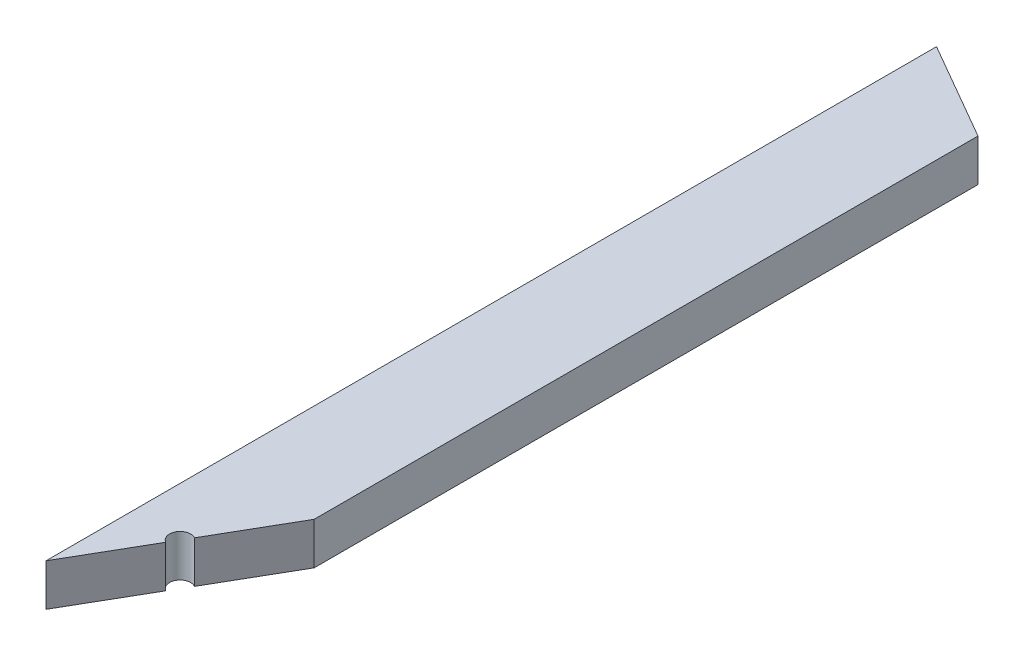
SolidWorks part; units mm, degrees
ref_plane "Front Plane" through (0, 0, 0) normal (0, 0, 1) x (1, 0, 0)
ref_plane "Top Plane" through (0, 0, 0) normal (0, 1, 0) x (1, 0, 0)
ref_plane "Right Plane" through (0, 0, 0) normal (1, 0, 0) x (0, 0, -1)
sketch "Sketch1" plane through (0, 0, 0) normal (0, 0, 1) x (1, 0, 0)
  line L1 (-44.45, -19.05) -> (44.45, -19.05)
  line L2 (-44.45, -19.05) -> (-44.45, 19.05)
  line L3 (-44.45, 19.05) -> (44.45, 19.05)
  line L4 (44.45, -19.05) -> (44.45, 19.05)
  line L5 (-44.45, -19.05) -> (44.45, 19.05) construction
  line L6 (-44.45, 19.05) -> (44.45, -19.05) construction
  point P0 (0, 0)
  dimension "D1" = 38.1
  dimension "D2" = 88.9
extrude "Boss-Extrude1" add sketch "Sketch1" along normal blind 806.5592
sketch "Sketch2" plane through (0, 19.05, 0) normal (0, 1, 0) x (1, 0, 0)
  line L0 (-44.45, 0) -> (44.45, 0)
  line L1 (44.45, 0) -> (44.45, -51.3264)
  line L2 (44.45, -806.5592) -> (44.45, 0) construction
  line L3 (44.45, -51.3264) -> (-44.45, 0)
  line L4 (-44.45, -806.5592) -> (44.45, -652.5799)
  line L5 (44.45, -652.5799) -> (44.45, -806.5592)
  line L6 (44.45, -806.5592) -> (-44.45, -806.5592)
  dimension "D1" = 30
  dimension "D2" = 60
extrude "Cut-Extrude1" cut sketch "Sketch2" against normal through all
sketch "Sketch3" plane through (0, 19.05, 0) normal (0, 1, 0) x (1, 0, 0)
  line L0 (44.45, -652.5799) -> (-44.45, -806.5592) construction
  circle A0 centre (0, -729.5696) radius 9.525
  dimension "D1" = 19.05
extrude "Cut-Extrude2" cut sketch "Sketch3" against normal through all
